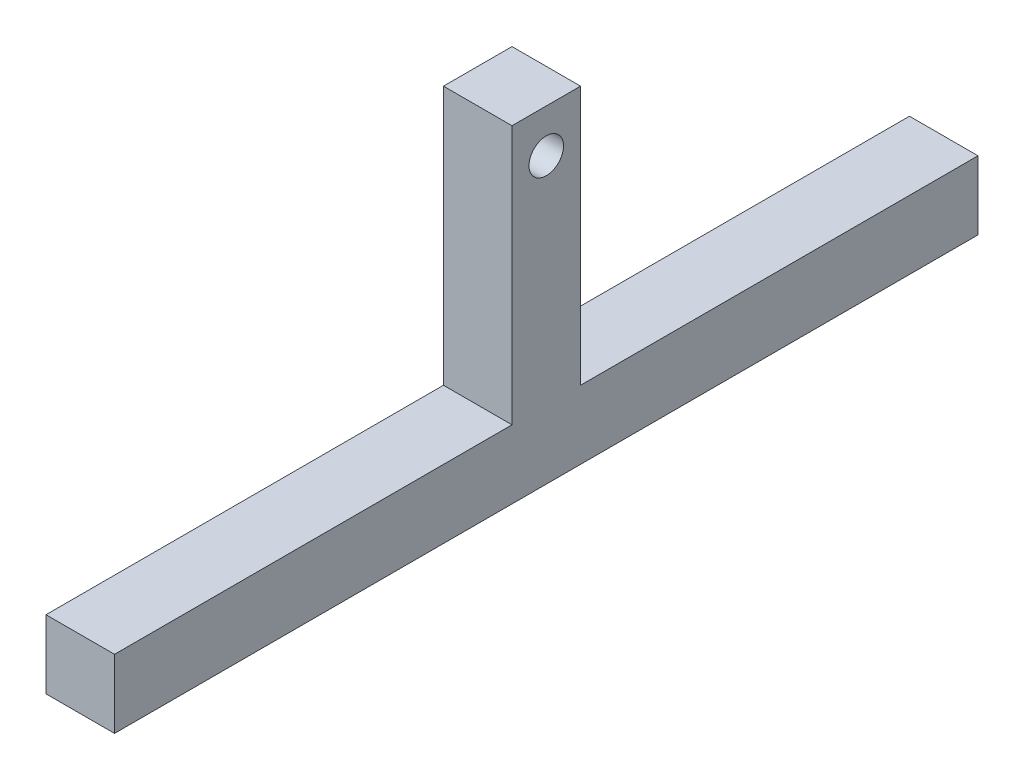
SolidWorks part; units mm, degrees
ref_plane "Front Plane" through (0, 0, 0) normal (0, 0, 1) x (1, 0, 0)
ref_plane "Top Plane" through (0, 0, 0) normal (0, 1, 0) x (1, 0, 0)
ref_plane "Right Plane" through (0, 0, 0) normal (1, 0, 0) x (0, 0, -1)
sketch "Sketch1" plane through (0, 0, 0) normal (1, 0, 0) x (0, 0, -1)
  line L1 (-100, 7.9375) -> (100, 7.9375)
  line L2 (-100, 7.9375) -> (-100, -7.9375)
  line L3 (-100, -7.9375) -> (100, -7.9375)
  line L4 (100, 7.9375) -> (100, -7.9375)
  line L5 (-7.9375, 7.9375) -> (7.9375, 7.9375)
  line L6 (-7.9375, 7.9375) -> (-7.9375, 67.9375)
  line L7 (-7.9375, 67.9375) -> (7.9375, 67.9375)
  line L8 (7.9375, 7.9375) -> (7.9375, 67.9375)
  point P4 (0, -7.9375)
  point P6 (100, 0)
  point P11 (0, 67.9375)
  dimension "D1" = 200
  dimension "D2" = 15.875
  dimension "D3" = 15.875
  dimension "D4" = 60
extrude "Boss-Extrude1" add sketch "Sketch1" along normal blind 15.875 contours L4 L1 L2 L3 | L1 L8 L7 L6
sketch "Sketch2" plane through (15.875, 0, 0) normal (1, 0, 0) x (0, 0, -1)
  line L0 (-7.9375, 67.9375) -> (7.9375, 67.9375) construction
  circle A0 centre (0, 57.9375) radius 4
  point P2 (0, 0)
  dimension "D1" = 8
  dimension "D2" = 10
extrude "Cut-Extrude1" cut sketch "Sketch2" against normal through all
